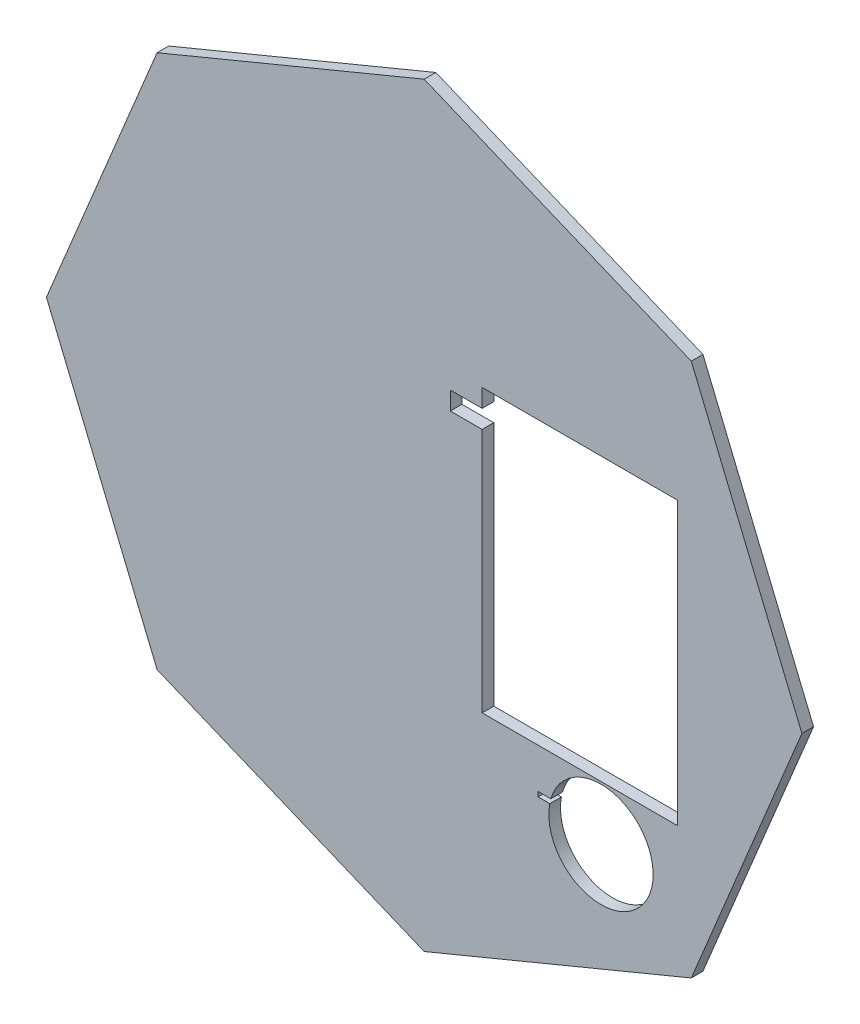
SolidWorks part; units mm, degrees
ref_plane "Plan de face" through (0, 0, 0) normal (0, 0, 1) x (1, 0, 0)
ref_plane "Plan de dessus" through (0, 0, 0) normal (0, 1, 0) x (1, 0, 0)
ref_plane "Plan de droite" through (0, 0, 0) normal (1, 0, 0) x (0, 0, -1)
sketch "Esquisse2" plane through (0, 0, 14.51) normal (0, 0, -1) x (-1, 0, 0)
  line L0 (-31.8518, 10.0537) -> (-31.8518, -17.3783)
  line L1 (-53.6958, 14.1177) -> (-31.8518, 14.1177)
  line L2 (-53.6958, 14.1177) -> (-53.6958, -17.3783)
  line L3 (-53.6958, -17.3783) -> (-31.8518, -17.3783)
  line L4 (-31.8518, 14.1177) -> (-31.8518, 12.0857)
  line L5 (-28.2958, 12.0857) -> (-31.8518, 12.0857)
  line L6 (-28.2958, 12.0857) -> (-28.2958, 10.0537)
  line L7 (-28.2958, 10.0537) -> (-31.8518, 10.0537)
  line L8 (-55.2238, -31.3523) -> (-25.3748, -43.7163)
  line L9 (-25.3748, -43.7163) -> (4.4742, -31.3523)
  line L10 (4.4742, -31.3523) -> (16.8382, -1.5033)
  line L11 (16.8382, -1.5033) -> (4.4742, 28.3457)
  line L12 (4.4742, 28.3457) -> (-25.3748, 40.7097)
  line L13 (-25.3748, 40.7097) -> (-55.2238, 28.3457)
  line L14 (-55.2238, 28.3457) -> (-67.5878, -1.5033)
  line L15 (-67.5878, -1.5033) -> (-55.2238, -31.3523)
  line L16 (-55.2238, -31.3523) -> (-25.3748, -43.7163)
  line L17 (-25.3748, -43.7163) -> (4.4742, -31.3523)
  line L18 (4.4742, -31.3523) -> (16.8382, -1.5033)
  line L19 (16.8382, -1.5033) -> (4.4742, 28.3457)
  line L20 (4.4742, 28.3457) -> (-25.3748, 40.7097)
  line L21 (-25.3748, 40.7097) -> (-55.2238, 28.3457)
  line L22 (-55.2238, 28.3457) -> (-67.5878, -1.5033)
  line L23 (-67.5878, -1.5033) -> (-55.2238, -31.3523)
  line L25 (-38.1018, -21.8603) -> (-39.5291, -21.8603)
  line L26 (-38.1018, -21.8603) -> (-38.1018, -22.3851)
  line L27 (-38.1018, -22.3851) -> (-39.4045, -22.3851)
  arc A0 (-39.5291, -21.8603) -> (-39.4045, -22.3851) centre (-45.131, -23.4673) ccw
  dimension "D1" = 0
extrude "Boss.-Extru.2" add sketch "Esquisse2" along normal blind 1.3
